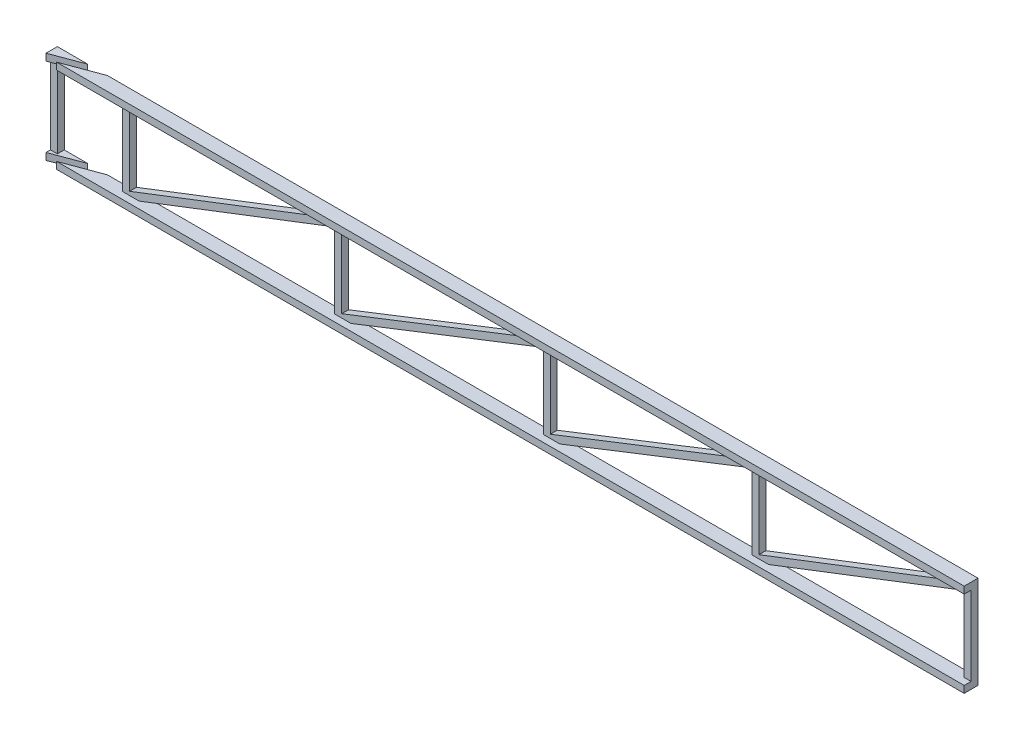
SolidWorks part; units mm, degrees
material "Balsa"
ref_plane "Front Plane" through (0, 0, 0) normal (0, 0, 1) x (1, 0, 0)
ref_plane "Top Plane" through (0, 0, 0) normal (0, 1, 0) x (1, 0, 0)
ref_plane "Right Plane" through (0, 0, 0) normal (1, 0, 0) x (0, 0, -1)
sketch "Sketch1" plane through (0, 0, 0) normal (0, 0, 1) x (1, 0, 0)
  line L0 (-18.175, 48.175) -> (18.175, 48.175)
  line L4 (405, 11.825) -> (405, 15)
  line L5 (-15, 45) -> (15, 45)
  line L7 (-15, 15) -> (15, 15)
  line L10 (405, 11.825) -> (405, 15)
  line L14 (-18.175, 11.825) -> (18.175, 11.825)
  line L16 (18.175, 48.175) -> (405, 48.175)
  line L17 (18.175, 11.825) -> (405, 11.825)
  line L18 (15, 45) -> (405, 45)
  line L19 (15, 15) -> (405, 15)
  line L20 (-18.175, 48.175) -> (-18.175, 45)
  line L21 (-18.175, 48.175) -> (-18.175, 11.825) construction
  line L22 (-15, 45) -> (-15, 15) construction
  line L23 (15, 45) -> (15, 15) construction
  line L24 (-18.175, 45) -> (-15, 45)
  line L25 (18.175, 48.175) -> (18.175, 11.825) construction
  line L26 (405, 45) -> (405, 48.175)
  line L27 (405, 45) -> (405, 48.175)
  line L28 (-18.175, 11.825) -> (-18.175, 15)
  line L29 (-18.175, 15) -> (-15, 15)
  point P4 (0, 30)
  dimension "D3" = 30
  dimension "D5" = 3.175
extrude "Boss-Extrude1" add sketch "Sketch1" along normal blind 3.175 contours L18 L26 L16 L0 L20 L24 L5 | L29 L28 L14 L17 L4 L19 L7
sketch "Sketch2" plane through (0, 0, 3.175) normal (0, 0, 1) x (1, 0, 0)
  line L0 (-18.175, 48.175) -> (405, 48.175) construction
  line L1 (-18.175, 11.825) -> (-15, 11.825)
  line L2 (-18.175, 11.825) -> (-18.175, 48.175)
  line L3 (-18.175, 48.175) -> (-15, 48.175)
  line L4 (-15, 11.825) -> (-15, 48.175)
  line L5 (-18.175, 11.825) -> (405, 11.825) construction
  line L6 (-15, 48.175) -> (15, 48.175)
  line L7 (-15, 48.175) -> (-15, 11.825)
  line L8 (-15, 11.825) -> (15, 11.825)
  line L9 (15, 48.175) -> (15, 11.825)
  line L10 (18.175, 30) -> (401.825, 30) construction
  line L11 (15, 48.175) -> (18.175, 48.175)
  line L12 (15, 48.175) -> (15, 11.825)
  line L13 (15, 11.825) -> (18.175, 11.825)
  line L14 (18.175, 48.175) -> (18.175, 11.825)
  line L15 (405, 48.175) -> (401.825, 48.175)
  line L16 (405, 48.175) -> (405, 11.825)
  line L17 (405, 11.825) -> (401.825, 11.825)
  line L18 (401.825, 48.175) -> (401.825, 11.825)
  line L19 (210, 30) -> (210, 38.7375) construction
  line L20 (18.175, 38.7375) -> (210, 38.7375) construction
  line L21 (114.0875, 38.7375) -> (114.0875, 45)
  line L22 (-18.175, 45) -> (405, 45) construction
  line L23 (210, 38.7375) -> (401.825, 38.7375) construction
  line L24 (305.9125, 38.7375) -> (305.9125, 45) construction
  line L25 (115.675, 11.825) -> (120.0251, 11.825)
  line L26 (115.675, 11.825) -> (112.5, 11.825)
  line L27 (115.675, 11.825) -> (115.675, 48.175)
  line L28 (114.1836, 48.175) -> (112.5, 48.175)
  line L29 (112.5, 11.825) -> (112.5, 48.175)
  line L30 (114.0875, 30) -> (113.3243, 38.7375) construction
  line L31 (115.675, 48.175) -> (112.5, 11.825) construction
  line L32 (211.5875, 11.825) -> (208.4125, 11.825)
  line L33 (211.5875, 11.825) -> (211.5875, 48.175)
  line L34 (211.5875, 48.175) -> (208.4125, 48.175)
  line L35 (208.4125, 11.825) -> (208.4125, 48.175)
  line L36 (211.5875, 11.825) -> (209.2368, 38.7375) construction
  line L37 (211.5875, 48.175) -> (208.4125, 11.825) construction
  line L38 (304.325, 11.825) -> (307.5, 11.825)
  line L39 (304.325, 11.825) -> (304.325, 48.175)
  line L40 (304.325, 48.175) -> (307.5, 48.175)
  line L41 (307.5, 11.825) -> (307.5, 48.175)
  line L42 (304.325, 11.825) -> (307.5, 48.175) construction
  line L43 (304.325, 48.175) -> (307.5, 11.825) construction
  line L44 (120.0251, 11.825) -> (208.4125, 46.4699)
  line L45 (111.3249, 11.825) -> (112.5417, 12.3019)
  line L46 (208.4125, 48.175) -> (204.0624, 48.175)
  line L47 (115.675, 13.5301) -> (204.0624, 48.175)
  point P36 (114.0875, 30)
  point P45 (305.9125, 30)
  line B0 (22.5897, 11.825) -> (112.5, 46.4737)
  line B1 (18.175, 13.5263) -> (108.0853, 48.175)
  line B2 (108.0853, 48.175) -> (112.5, 48.175)
  line B3 (18.175, 11.825) -> (22.5897, 11.825)
  line B4 (211.5875, 11.825) -> (215.9376, 11.825)
  line B5 (215.9376, 11.825) -> (304.325, 46.4699)
  line B6 (304.325, 48.175) -> (299.9749, 48.175)
  line B7 (211.5875, 13.5301) -> (299.9749, 48.175)
  line B8 (311.9147, 11.825) -> (401.825, 46.4737)
  line B9 (307.5, 13.5263) -> (397.4103, 48.175)
  line B10 (397.4103, 48.175) -> (401.825, 48.175)
  line B11 (307.5, 11.825) -> (311.9147, 11.825)
  dimension "D1" = 3.175
  dimension "D2" = 30
  dimension "D3" = 3.175
  dimension "D4" = 3.175
  dimension "D5" = 3.175
  dimension "D6" = 3.175
  dimension "D7" = 3.175
  dimension "D8" = 0
  dimension "D10" = 0
  dimension "D9" = 0
  dimension "D11" = 0
sketch_block_instance "Block1-1"
sketch_block "Block1"
sketch_block_instance "Block2-1"
sketch_block "Block2"
sketch_block_instance "Block1-3"
extrude "Boss-Extrude2" add sketch "Sketch2" along normal blind 3.175
sketch "Sketch3" plane through (405, 0, 0) normal (1, 0, 0) x (0, 0, -1)
  line L1 (-6.35, 11.825) -> (-3.175, 11.825)
  line L2 (-6.35, 11.825) -> (-6.35, 8.65)
  line L3 (-6.35, 8.65) -> (-3.175, 8.65)
  line L4 (-3.175, 11.825) -> (-3.175, 8.65)
  line L5 (-6.35, 48.175) -> (-3.175, 48.175)
  line L6 (-6.35, 48.175) -> (-6.35, 51.35)
  line L7 (-6.35, 51.35) -> (-3.175, 51.35)
  line L8 (-3.175, 48.175) -> (-3.175, 51.35)
  dimension "D1" = 3.175
  dimension "D2" = 3.175
extrude "Boss-Extrude8" add sketch "Sketch3" against normal up to surface (423.175 mm away) separate body contours L8 L7 L6 M2 | L4 L2 L3 M4 up to face at (-18.175, 30, 2.3812)
sketch "Sketch4" plane through (405, 0, 0) normal (1, 0, 0) x (0, 0, -1)
  line L1 (-3.175, 48.175) -> (0, 48.175)
  line L2 (-3.175, 48.175) -> (-3.175, 11.825)
  line L3 (-3.175, 11.825) -> (0, 11.825)
  line L4 (0, 48.175) -> (0, 11.825)
extrude "Cut-Extrude1" cut sketch "Sketch4" against normal through all
sketch "Sketch5" plane through (0, 8.65, 0) normal (0, -1, 0) x (1, 0, 0)
  line L17 (193.4125, 3.175) -> (193.4125, -106.4437) construction
  line L22 (-26.8415, 33.7017) -> (-103.7417, -72.6912)
  line L24 (377.5812, -136.0518) -> (376.4702, -139.0261)
  line L25 (-18.175, 6.35) -> (406.5875, 6.35)
  line L26 (405, 3.175) -> (-18.175, 3.175)
  line L27 (405, 6.35) -> (-18.175, 6.35)
  line L28 (377.5812, -136.0518) -> (4.8614, 3.175)
  line L29 (-12.7117, 6.35) -> (-26.8415, 33.7017)
  line L30 (403.4125, 6.35) -> (403.4125, -137.0625)
  line L31 (376.4702, -139.0261) -> (-4.212, 3.175)
  line L32 (-12.7117, 6.35) -> (-3.6383, 6.35)
  line L33 (406.5875, 6.35) -> (406.5875, -140.2375)
  line L34 (4.8614, 3.175) -> (-3.6383, 6.35)
  line L35 (-4.212, 3.175) -> (-12.7117, 6.35)
  line L36 (405, 6.35) -> (405, -138.65)
  arc A1 (372.1591, -137.4157) -> (373.2701, -134.4414) centre (380, -138.65) cw
extrude "Cut-Extrude7" cut sketch "Sketch5" against normal blind 3.175 contours L35 L26 L34 M6
sketch "Sketch9" plane through (0, 51.35, 0) normal (0, 1, 0) x (1, 0, 0)
  line L0 (391.037, -3.175) -> (399.5367, -6.35) construction
  line L1 (391.037, -3.175) -> (399.5367, -6.35)
  line L2 (381.9636, -3.175) -> (390.4633, -6.35) construction
  line L3 (391.037, -3.175) -> (399.5367, -6.35)
  line L4 (381.9636, -3.175) -> (390.4633, -6.35)
  line L5 (381.9636, -3.175) -> (391.037, -3.175)
  line L6 (399.5367, -6.35) -> (390.4633, -6.35)
  line L7 (-4.212, -3.175) -> (-12.7117, -6.35) construction
  line L8 (4.8614, -3.175) -> (-3.6383, -6.35) construction
  line L9 (-4.212, -3.175) -> (-12.7117, -6.35)
  line L10 (4.8614, -3.175) -> (-3.6383, -6.35)
  line L11 (-12.7117, -6.35) -> (-3.6383, -6.35)
extrude "Cut-Extrude8" cut sketch "Sketch9" against normal blind 3.175 contours L10 L9 M1 M3
ref_plane "Plane4" through (193.4125, 0, 0) normal (-1, 0, 0) x (0, 0, 1)
sketch "Sketch10" plane through (0, 0, 6.35) normal (0, 0, 1) x (1, 0, 0)
  line L0 (-3.6383, 51.35) -> (-3.6383, 48.175) construction
  line L1 (-3.6383, 48.175) -> (405, 48.175) construction
  line L2 (405, 48.175) -> (405, 51.35) construction
  line L3 (405, 51.35) -> (-3.6383, 51.35) construction
  line L4 (-3.6383, 11.825) -> (-3.6383, 8.65) construction
  line L5 (-3.6383, 8.65) -> (405, 8.65) construction
  line L6 (405, 8.65) -> (405, 11.825) construction
  line L7 (405, 11.825) -> (-3.6383, 11.825) construction
  line L8 (-3.6383, 51.35) -> (-3.6383, 48.175)
  line L9 (-3.6383, 48.175) -> (405, 48.175)
  line L10 (405, 48.175) -> (405, 51.35)
  line L11 (405, 51.35) -> (-3.6383, 51.35)
  line L12 (-3.6383, 11.825) -> (-3.6383, 8.65)
  line L13 (-3.6383, 8.65) -> (405, 8.65)
  line L14 (405, 8.65) -> (405, 11.825)
  line L15 (405, 11.825) -> (-3.6383, 11.825)
extrude "Boss-Extrude9" add sketch "Sketch10" along normal blind 3.175
sketch "Sketch11" plane through (0, 51.35, 0) normal (0, 1, 0) x (1, 0, 0)
  line L0 (376.8933, 139.1842) -> (-18.175, -8.3908) construction
  line L1 (-18.175, -8.3908) -> (-18.175, -9.525) construction
  line L2 (-18.175, -9.525) -> (-12.138, -9.525) construction
  line L3 (-12.138, -9.525) -> (378.0043, 136.2099) construction
  line L4 (378.0043, 136.2099) -> (376.8933, 139.1842) construction
  line L5 (405, -6.35) -> (-18.175, -6.35) construction
  line L6 (-18.175, -6.35) -> (-18.175, -9.525) construction
  line L7 (-18.175, -9.525) -> (405, -9.525) construction
  line L8 (405, -9.525) -> (405, -6.35) construction
  line L9 (376.8933, 139.1842) -> (-18.175, -8.3908)
  line L10 (-18.175, -8.3908) -> (-18.175, -9.525)
  line L11 (-18.175, -9.525) -> (-12.138, -9.525)
  line L12 (-12.138, -9.525) -> (378.0043, 136.2099)
  line L13 (378.0043, 136.2099) -> (376.8933, 139.1842)
  line L14 (405, -6.35) -> (-18.175, -6.35)
  line L15 (-18.175, -6.35) -> (-18.175, -9.525)
  line L16 (-18.175, -9.525) -> (405, -9.525)
  line L17 (405, -9.525) -> (405, -6.35)
extrude "Boss-Extrude10" add sketch "Sketch11" against normal blind 3.175 contours L15 L9 M1 | L16 L17 L14 L12
sketch "Sketch12" plane through (0, 8.65, 0) normal (0, -1, 0) x (1, 0, 0)
  line L0 (-18.175, 9.525) -> (-18.175, 8.3908) construction
  line L1 (-18.175, 8.3908) -> (376.8933, -139.1842) construction
  line L2 (376.8933, -139.1842) -> (378.0043, -136.2099) construction
  line L3 (378.0043, -136.2099) -> (-12.138, 9.525) construction
  line L4 (-12.138, 9.525) -> (-18.175, 9.525) construction
  line L5 (-18.175, 6.35) -> (405, 6.35) construction
  line L6 (405, 6.35) -> (405, 9.525) construction
  line L7 (405, 9.525) -> (-18.175, 9.525) construction
  line L8 (-18.175, 9.525) -> (-18.175, 6.35) construction
  line L9 (-18.175, 9.525) -> (-18.175, 8.3908)
  line L10 (-18.175, 8.3908) -> (376.8933, -139.1842)
  line L11 (376.8933, -139.1842) -> (378.0043, -136.2099)
  line L12 (378.0043, -136.2099) -> (-12.138, 9.525)
  line L13 (-12.138, 9.525) -> (-18.175, 9.525)
  line L14 (-18.175, 6.35) -> (405, 6.35)
  line L15 (405, 6.35) -> (405, 9.525)
  line L16 (405, 9.525) -> (-18.175, 9.525)
  line L17 (-18.175, 9.525) -> (-18.175, 6.35)
extrude "Boss-Extrude11" add sketch "Sketch12" against normal blind 3.175 contours L16 L12 M5 | L10 L17 L14
